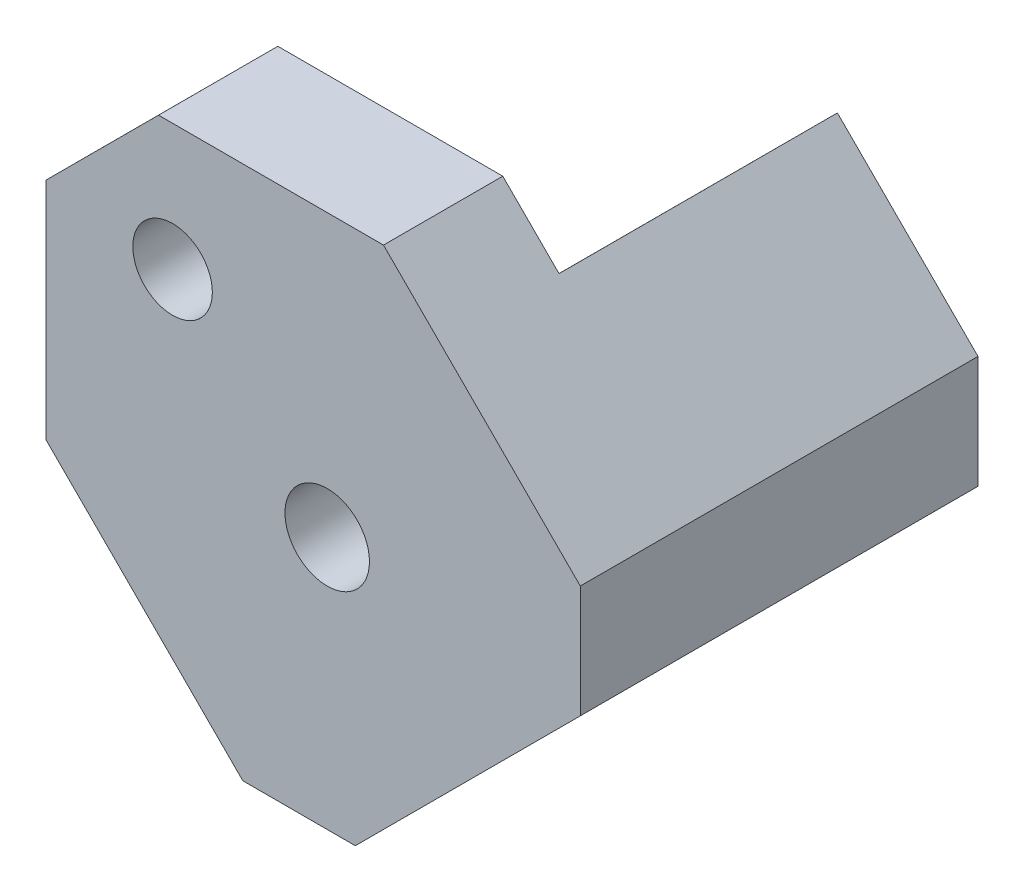
SolidWorks part; units mm, degrees
material "AISI 1018 Steel, Cold Rolled"
ref_plane "Front" through (0, 0, 0) normal (0, 0, 1) x (1, 0, 0)
ref_plane "Top" through (0, 0, 0) normal (0, 1, 0) x (1, 0, 0)
ref_plane "Right" through (0, 0, 0) normal (1, 0, 0) x (0, 0, -1)
sketch "Sketch1" plane through (0, 0, 0) normal (0, 0, 1) x (1, 0, 0)
  line L0 (128.5747, -68.8545) -> (128.5726, -86.815)
  line L1 (43.2597, -91.2952) -> (74.6869, -122.7298)
  line L2 (61.2265, -37.4158) -> (43.2639, -55.3742)
  line L3 (61.2265, -37.4158) -> (97.1475, -37.4199)
  line L4 (43.2639, -55.3742) -> (43.2597, -91.2952)
  line L5 (92.6474, -122.7318) -> (74.6869, -122.7298)
  line L7 (128.5726, -86.815) -> (92.6474, -122.7318)
  line L10 (97.1475, -37.4199) -> (128.5747, -68.8545)
  point P2 (79.1891, -19.4573)
  point P10 (83.6661, -131.7111)
  point P13 (25.3013, -73.3326)
  point P14 (137.5539, -77.8358)
  dimension "D4" = 25.4
  dimension "D5" = 76.2
  dimension "D7" = 25.4
  dimension "D1" = 82.55
  dimension "D9" = 12.7
  dimension "D10" = 12.7
extrude "Base-Extrude" add sketch "Sketch1" along normal blind 63.5
hole_wizard "1/2-20 Tapped Hole1" positions "Sketch4" profile "Sketch3" tap size "1/2-20" standard "Ansi Inch" end condition through all
sketch "Sketch4" plane through (0, 0, 63.5) normal (0, 0, 1) x (1, 0, 0)
  line L5 (128.5747, -68.8545) -> (97.1475, -37.4199) construction
  line L6 (61.2265, -37.4158) -> (43.2639, -55.3742) construction
  point P0 (63.4692, -57.6216)
  dimension "D1" = 38.1
  dimension "D2" = 15.875
sketch "Sketch3" plane through (63.4692, -57.6216, 63.5) normal (1, 0, 0) x (0, -1, 0)
  line L0 (0, 0) -> (0, 63.5)
  line L1 (0, 63.5) -> (6.35, 63.5)
  line L2 (6.35, 63.5) -> (6.35, 0)
  line L5 (6.35, 0) -> (0, 0)
  line L11 (0, -6.35) -> (0, 107.95) construction
  dimension "Thread Major Dia." = 12.7
  dimension "Thru Tap Drill Depth" = 63.5
hole_wizard "17/32 (0.53125) Diameter Hole2" positions "Sketch8" profile "Sketch7" hole size "17/32" standard "Ansi Inch" end condition through all
sketch "Sketch8" plane through (0, 0, 63.5) normal (0, 0, 1) x (1, 0, 0)
  line L1 (128.5747, -68.8545) -> (97.1475, -37.4199) construction
  line L2 (61.2265, -37.4158) -> (43.2639, -55.3742) construction
  point P0 (88.162, -82.3202)
  dimension "D1" = 38.1
  dimension "D2" = 50.8
sketch "Sketch7" plane through (88.162, -82.3202, 63.5) normal (1, 0, 0) x (0, -1, 0)
  line L0 (0, 0) -> (0, 63.5)
  line L1 (0, 63.5) -> (6.7469, 63.5)
  line L2 (6.7469, 63.5) -> (6.7469, 0)
  line L5 (6.7469, 0) -> (0, 0)
  line L11 (0, -6.35) -> (0, 107.95) construction
  dimension "Thru Hole Dia." = 13.4937
  dimension "Thru Hole Depth" = 63.5
sketch "Sketch10" plane through (-24.0127, -24.0071, 0) normal (-0.7072, -0.707, 0) x (0, 0, 1)
  line L1 (0, -107.8486) -> (44.45, -107.8486)
  line L2 (0, -107.8486) -> (0, -69.7486)
  line L3 (0, -69.7486) -> (44.45, -69.7486)
  line L4 (44.45, -107.8486) -> (44.45, -69.7486)
  line L5 (63.5, -139.5986) -> (63.5, -95.1486) construction
  line L6 (0, -139.5986) -> (0, -95.1486) construction
  line L7 (63.5, -69.7486) -> (0, -69.7486) construction
  line L8 (63.5, -152.2986) -> (0, -152.2986) construction
  dimension "D1" = 19.05
  dimension "D2" = 44.45
extrude "Cut-Extrude1" cut sketch "Sketch10" against normal through all
hole_wizard "1/2-20 Tapped Hole3" positions "Sketch12" profile "Sketch11" tap size "1/2-20" standard "Ansi Inch" end condition through all
sketch "Sketch12" plane through (107.6789, -107.7039, 0) normal (0.707, -0.7072, 0) x (0.7072, 0.707, 0)
  line L0 (-33.9552, 63.5) -> (-33.9552, 0) construction
  line L1 (-21.2552, 0) -> (29.5448, 0) construction
  point P0 (-14.9052, 25.4)
  dimension "D1" = 19.05
  dimension "D2" = 25.4
sketch "Sketch11" plane through (97.1381, -118.2422, 25.4) normal (0, 0, 1) x (0.7072, 0.707, 0)
  line L0 (0, 0) -> (0, 95.253)
  line L1 (0, 95.253) -> (6.35, 95.253)
  line L2 (6.35, 95.253) -> (6.35, 0)
  line L5 (6.35, 0) -> (0, 0)
  line L11 (0, -6.35) -> (0, 107.95) construction
  dimension "Thread Major Dia." = 12.7
  dimension "Thru Tap Drill Depth" = 95.253
